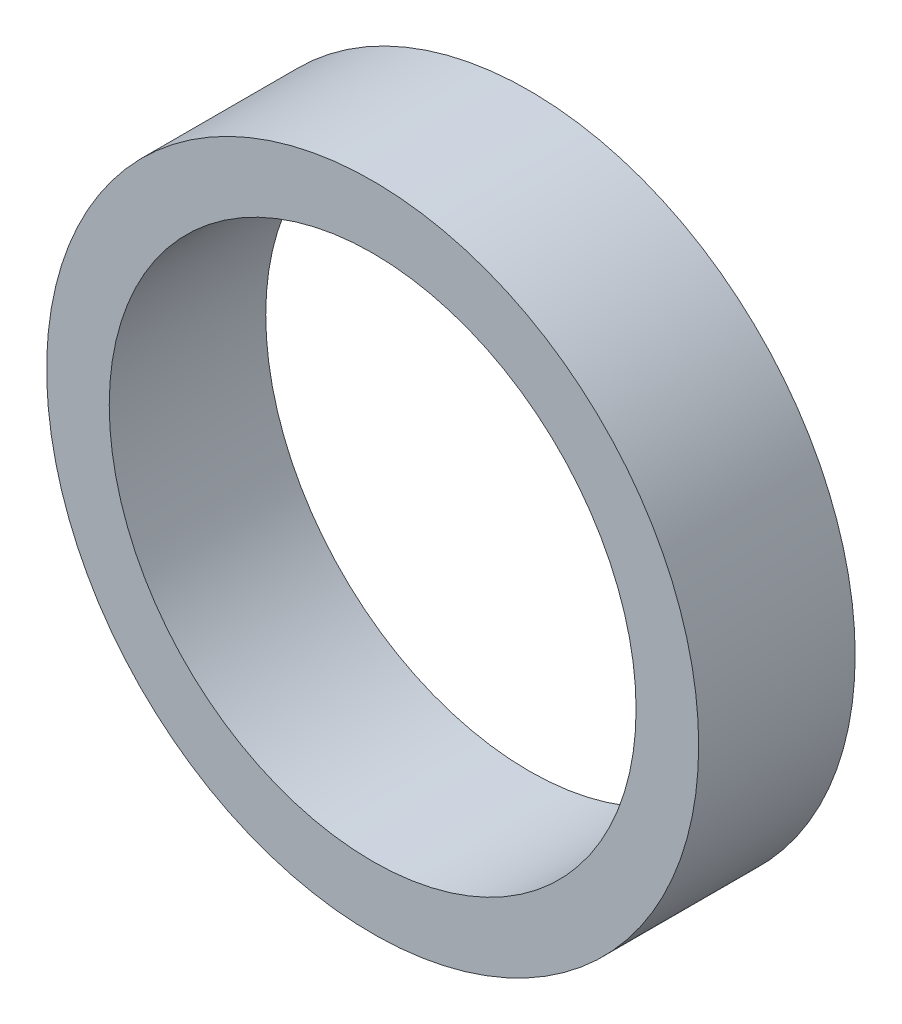
SolidWorks part; units mm, degrees
ref_plane "Спереди" through (0, 0, 0) normal (0, 0, 1) x (1, 0, 0)
ref_plane "Сверху" through (0, 0, 0) normal (0, 1, 0) x (1, 0, 0)
ref_plane "Справа" through (0, 0, 0) normal (1, 0, 0) x (0, 0, -1)
sketch "Эскиз1" plane through (0, 0, 0) normal (0, 0, 1) x (1, 0, 0)
  circle A0 centre (0, 0) radius 0.606
  circle A1 centre (0, 0) radius 0.75
  dimension "D1" = 1.5
  dimension "D2" = 1.212
extrude "Бобышка-Вытянуть1" add sketch "Эскиз1" along normal blind 0.36
